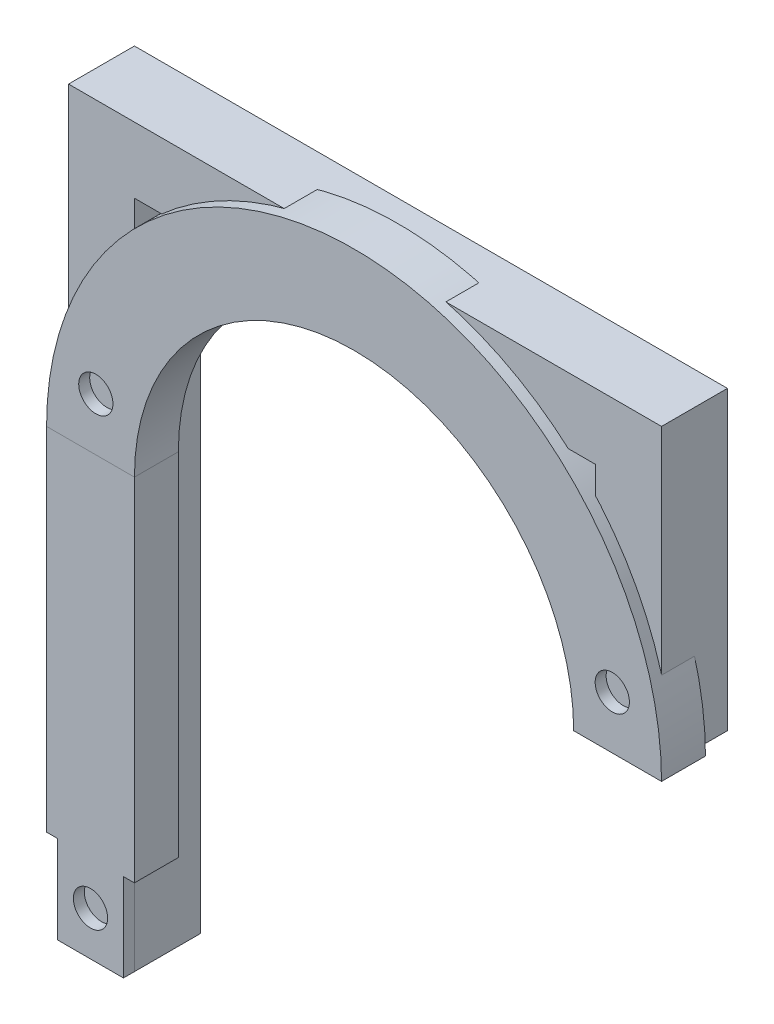
SolidWorks part; units mm, degrees
material "1060 Alloy"
ref_plane "Front Plane" through (0, 0, 0) normal (0, 0, 1) x (1, 0, 0)
ref_plane "Top Plane" through (0, 0, 0) normal (0, 1, 0) x (1, 0, 0)
ref_plane "Right Plane" through (0, 0, 0) normal (1, 0, 0) x (0, 0, -1)
sketch "Sketch8" plane through (0, 0, 0) normal (0, 0, 1) x (1, 0, 0)
  line L0 (0, 0) -> (0, 101.6)
  line L1 (0, 101.6) -> (76.2, 101.6)
  line L2 (76.2, 101.6) -> (76.2, 63.5)
  dimension "D1" = 101.6
  dimension "D2" = 76.2
  dimension "D3" = 38.1
extrude "Extrude-Thin3" add sketch "Sketch8" along normal mid plane 9.525 separate body thin thin type mid plane wall 9.525
sketch "Sketch37" plane through (0, 0, 0) normal (0, 0, 1) x (1, 0, 0)
  line L0 (0, 0) -> (0, 63.5)
  arc A1 (0, 63.5) -> (76.2, 63.5) centre (38.1, 63.5) cw
  dimension "D1" = 38.1
  dimension "D2" = 63.5
  dimension "D3" = 76.2
sketch "Sketch38" plane through (0, 0, 0) normal (0, 1, 0) x (1, 0, 0)
  line L1 (-6.35, 0) -> (6.35, 0)
  line L2 (-6.35, 0) -> (-6.35, -6.35)
  line L3 (-6.35, -6.35) -> (6.35, -6.35)
  line L4 (6.35, 0) -> (6.35, -6.35)
  line L5 (-6.35, 0) -> (6.35, -6.35) construction
  line L6 (-6.35, -6.35) -> (6.35, 0) construction
  point P0 (0, 0)
  point P8 (0, 0)
  dimension "D1" = 6.35
  dimension "D2" = 12.7
sweep "Sweep5" add profiles "Sketch38" path "Sketch37"
sketch "Sketch39" plane through (0, 0, 0) normal (0, 0, 1) x (1, 0, 0)
  line L0 (81.6519, 72.39) -> (69.2085, 69.85) construction
  line L1 (38.1, 107.95) -> (38.1, 63.5) construction
  circle A0 centre (75.4302, 71.12) radius 2.4765
  arc A1 (82.55, 63.5) -> (-6.35, 63.5) centre (38.1, 63.5) ccw construction
  arc A2 (69.85, 63.5) -> (6.35, 63.5) centre (38.1, 63.5) ccw construction
  circle A3 centre (0.7698, 71.12) radius 2.4765
  point P14 (75.4302, 71.12)
  dimension "D1" = 4.953
  dimension "D3" = 12.7
  dimension "D2" = 6.35
extrude "Cut-Extrude1" cut sketch "Sketch39" along normal through all
sketch "Sketch42" plane through (0, 0, 0) normal (0, -1, 0) x (1, 0, 0)
  line L1 (-6.35, 6.35) -> (6.35, 6.35)
  line L2 (-6.35, 6.35) -> (-6.35, 0)
  line L3 (-6.35, 0) -> (6.35, 0)
  line L4 (6.35, 6.35) -> (6.35, 0)
extrude "Cut-Extrude2" cut sketch "Sketch42" against normal blind 12.7
sketch "Sketch43" plane through (0, 12.7, 0) normal (0, -1, 0) x (1, 0, 0)
  line L1 (-4.7625, 1.5875) -> (4.7625, 1.5875)
  line L2 (-4.7625, 1.5875) -> (-4.7625, 6.35)
  line L3 (-4.7625, 6.35) -> (4.7625, 6.35)
  line L4 (4.7625, 1.5875) -> (4.7625, 6.35)
  line L5 (6.35, 0) -> (6.35, 6.35) construction
  line L6 (6.35, 6.35) -> (-6.35, 6.35) construction
  dimension "D1" = 4.7625
  dimension "D2" = 9.525
  dimension "D3" = 1.5875
extrude "Boss-Extrude4" add sketch "Sketch43" along normal blind 12.7
sketch "Sketch44" plane through (0, 0, 6.35) normal (0, 0, 1) x (1, 0, 0)
  line L2 (4.7625, 0) -> (-4.7625, 0) construction
  line L3 (4.7625, 0) -> (4.7625, 12.7) construction
  circle A0 centre (0, 6.35) radius 2.4765
  point P7 (0, 0)
  point P10 (4.7625, 6.35)
  dimension "D1" = 4.953
extrude "Cut-Extrude3" cut sketch "Sketch44" against normal through all
